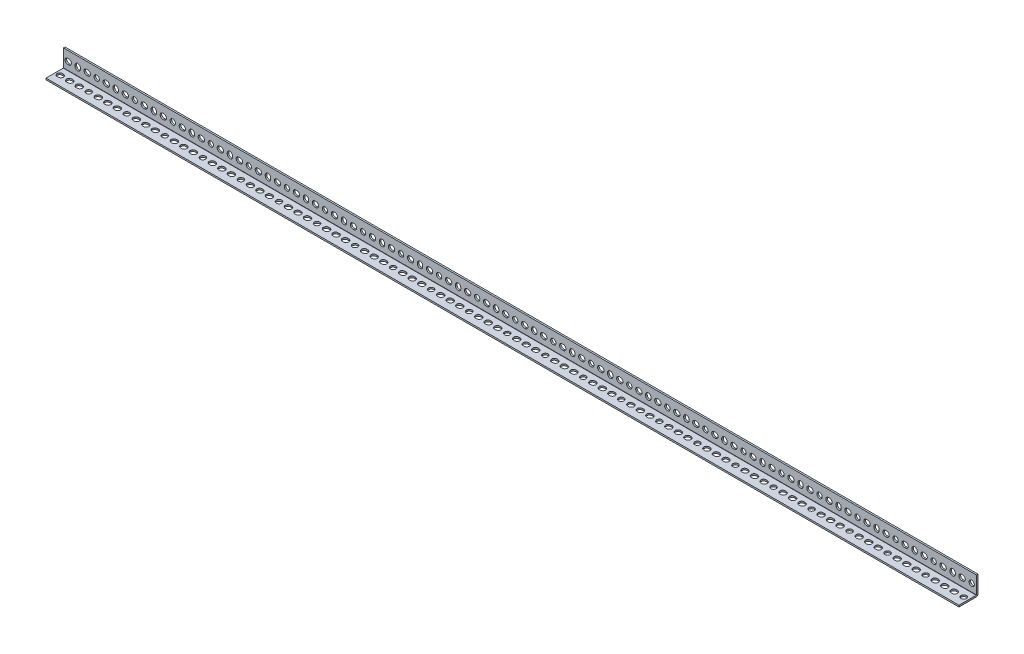
SolidWorks part; units mm, degrees
ref_plane "Front Plane" through (0, 0, 0) normal (0, 0, 1) x (1, 0, 0)
ref_plane "Top Plane" through (0, 0, 0) normal (0, 1, 0) x (1, 0, 0)
ref_plane "Right Plane" through (0, 0, 0) normal (1, 0, 0) x (0, 0, -1)
sketch "Sketch1" plane through (0, 0, 0) normal (1, 0, 0) x (0, 0, -1)
  line L0 (-19.05, -15.875) -> (15.875, -15.875) construction
  line L1 (15.875, -15.875) -> (15.875, 19.05) construction
  line L2 (15.875, 19.05) -> (19.05, 19.05) construction
  line L3 (19.05, 19.05) -> (19.05, -19.05) construction
  line L4 (19.05, -19.05) -> (-19.05, -19.05) construction
  line L5 (-19.05, -19.05) -> (-19.05, -15.875) construction
  line L6 (0, -19.05) -> (0, 19.05) construction
  line L7 (19.05, 0) -> (-19.05, 0) construction
  arc A0 (15.494, -15.875) -> (15.875, -15.494) centre (15.494, -15.494) ccw construction
  dimension "D1" = 0.381
  dimension "Thickness | T" = 3.175
  dimension "Width (B)" = 38.1
  dimension "Width (A)" = 38.1
sketch "Sketch2" plane through (0, 0, 0) normal (0, 0, 1) x (1, 0, 0)
  line L0 (-914.4, 0) -> (914.4, 0) construction
  line L1 (-914.4, 19.05) -> (914.4, 19.05) construction
  line L2 (-914.4, 19.05) -> (-914.4, -19.05) construction
  line L3 (-914.4, -19.05) -> (914.4, -19.05) construction
  line L4 (914.4, 19.05) -> (914.4, -19.05) construction
  line L5 (0, 19.05) -> (0, -19.05) construction
  line L6 (886.841, 0) -> (884.809, 0) construction
  line L7 (-914.4, -15.875) -> (914.4, -15.875) construction
  line L8 (886.841, -5.334) -> (884.809, -5.334) construction
  line L9 (886.841, 5.334) -> (884.809, 5.334) construction
  line L10 (866.775, -1.016) -> (866.775, 1.016) construction
  line L11 (861.441, -1.016) -> (861.441, 1.016) construction
  line L12 (872.109, -1.016) -> (872.109, 1.016) construction
  line L14 (848.741, 0) -> (846.709, 0) construction
  line L15 (848.741, -5.334) -> (846.709, -5.334) construction
  line L16 (848.741, 5.334) -> (846.709, 5.334) construction
  circle A0 centre (904.875, 0) radius 5.334 construction
  arc A2 (886.841, -5.334) -> (886.841, 5.334) centre (886.841, 0) ccw construction
  arc A3 (884.809, 5.334) -> (884.809, -5.334) centre (884.809, 0) ccw construction
  arc A4 (861.441, -1.016) -> (872.109, -1.016) centre (866.775, -1.016) ccw construction
  arc A5 (872.109, 1.016) -> (861.441, 1.016) centre (866.775, 1.016) ccw construction
  arc A6 (848.741, -5.334) -> (848.741, 5.334) centre (848.741, 0) ccw construction
  arc A7 (846.709, 5.334) -> (846.709, -5.334) centre (846.709, 0) ccw construction
  point P15 (819.15, 0)
  point P16 (-819.15, 0)
  point P17 (885.825, 0)
  point P24 (910.209, 0)
  point P26 (866.775, 0)
  point P37 (847.725, 0)
  dimension "Mounting Hole Diameter" = 10.668
  dimension "Length | L" = 1828.8
  dimension "D1" = 9.525
  dimension "D2" = 85.725
  dimension "D3" = 12.7
  dimension "D4" = 19.05
  dimension "Mounting Hole Center to Center" = 19.05
  dimension "D5" = 19.05
  dimension "D7" = 19.05
sketch "Sketch3" plane through (0, 0, 0) normal (0, 1, 0) x (1, 0, 0)
  line L0 (886.841, 0) -> (884.809, 0) construction
  line L1 (-914.4, 19.05) -> (914.4, 19.05) construction
  line L2 (-914.4, 19.05) -> (-914.4, -19.05) construction
  line L3 (-914.4, -19.05) -> (914.4, -19.05) construction
  line L4 (914.4, 19.05) -> (914.4, -19.05) construction
  line L5 (-914.4, 15.875) -> (914.4, 15.875) construction
  line L6 (886.841, -5.334) -> (884.809, -5.334) construction
  line L7 (865.759, 0) -> (867.791, 0) construction
  line L8 (886.841, 5.334) -> (884.809, 5.334) construction
  line L12 (846.709, 0) -> (848.741, 0) construction
  line L13 (846.709, 5.334) -> (848.741, 5.334) construction
  line L14 (846.709, -5.334) -> (848.741, -5.334) construction
  line L16 (886.841, 5.334) -> (904.875, 5.334) construction
  line L17 (865.759, 5.334) -> (867.791, 5.334) construction
  line L18 (865.759, -5.334) -> (867.791, -5.334) construction
  circle A0 centre (904.875, 0) radius 5.334 construction
  arc A2 (886.841, -5.334) -> (886.841, 5.334) centre (886.841, 0) ccw construction
  arc A3 (884.809, 5.334) -> (884.809, -5.334) centre (884.809, 0) ccw construction
  arc A6 (846.709, 5.334) -> (846.709, -5.334) centre (846.709, 0) ccw construction
  arc A7 (848.741, -5.334) -> (848.741, 5.334) centre (848.741, 0) ccw construction
  arc A10 (865.759, 5.334) -> (865.759, -5.334) centre (865.759, 0) ccw construction
  arc A11 (867.791, -5.334) -> (867.791, 5.334) centre (867.791, 0) ccw construction
  point P9 (885.825, 0)
  point P21 (910.209, 0)
  point P28 (866.775, 0)
  point P42 (847.725, 0)
  dimension "D1" = 19.05
sketch "Sketch4" plane through (0, 0, 0) normal (1, 0, 0) x (0, 0, -1)
  line L0 (-19.05, -15.875) -> (15.494, -15.875)
  line L1 (15.875, -15.494) -> (15.875, 19.05)
  line L2 (15.875, 19.05) -> (19.05, 19.05)
  line L3 (19.05, 19.05) -> (19.05, -15.494)
  line L4 (15.494, -19.05) -> (-19.05, -19.05)
  line L5 (-19.05, -19.05) -> (-19.05, -15.875)
  arc A0 (15.494, -15.875) -> (15.875, -15.494) centre (15.494, -15.494) ccw
  arc A1 (19.05, -15.494) -> (15.494, -19.05) centre (15.494, -15.494) cw
extrude "Boss-Extrude1" add sketch "Sketch4" along normal up to vertex (914.4 mm away) and the other way up to vertex (914.4 mm away) up to point (914.4, 0, 0) other way up to point (-914.4, 0, 0)
sketch "Sketch5" plane through (0, 0, 0) normal (0, 0, 1) x (1, 0, 0)
  line L0 (884.809, 0) -> (886.841, 0) construction
  line L1 (884.809, 5.334) -> (886.841, 5.334)
  line L2 (884.809, -5.334) -> (886.841, -5.334)
  line L3 (866.775, 1.016) -> (866.775, -1.016) construction
  line L4 (872.109, 1.016) -> (872.109, -1.016)
  line L5 (861.441, 1.016) -> (861.441, -1.016)
  line L6 (846.709, 0) -> (848.741, 0) construction
  line L7 (846.709, 5.334) -> (848.741, 5.334)
  line L8 (846.709, -5.334) -> (848.741, -5.334)
  circle A0 centre (904.875, 0) radius 5.334
  arc A1 (884.809, 5.334) -> (884.809, -5.334) centre (884.809, 0) ccw
  arc A2 (886.841, -5.334) -> (886.841, 5.334) centre (886.841, 0) ccw
  arc A3 (872.109, 1.016) -> (861.441, 1.016) centre (866.775, 1.016) ccw
  arc A4 (861.441, -1.016) -> (872.109, -1.016) centre (866.775, -1.016) ccw
  arc A5 (846.709, 5.334) -> (846.709, -5.334) centre (846.709, 0) ccw
  arc A6 (848.741, -5.334) -> (848.741, 5.334) centre (848.741, 0) ccw
  point P5 (885.825, 0)
  point P13 (866.775, 0)
  point P28 (847.725, 0)
extrude "Cut-Extrude1" cut sketch "Sketch5" against normal through all
pattern_linear "LPattern1" count 25 spacing 76.2 along (-1, 0, 0) of "Cut-Extrude1"
sketch "Sketch6" plane through (0, 0, 0) normal (0, 1, 0) x (1, 0, 0)
  line L0 (884.809, 0) -> (886.841, 0) construction
  line L1 (884.809, 5.334) -> (886.841, 5.334)
  line L2 (884.809, -5.334) -> (886.841, -5.334)
  line L3 (865.759, 0) -> (867.791, 0) construction
  line L6 (846.709, 0) -> (848.741, 0) construction
  line L7 (846.709, 5.334) -> (848.741, 5.334)
  line L8 (846.709, -5.334) -> (848.741, -5.334)
  line L11 (865.759, 5.334) -> (867.791, 5.334)
  line L12 (865.759, -5.334) -> (867.791, -5.334)
  circle A0 centre (904.875, 0) radius 5.334
  arc A1 (884.809, 5.334) -> (884.809, -5.334) centre (884.809, 0) ccw
  arc A2 (886.841, -5.334) -> (886.841, 5.334) centre (886.841, 0) ccw
  arc A5 (846.709, 5.334) -> (846.709, -5.334) centre (846.709, 0) ccw
  arc A6 (848.741, -5.334) -> (848.741, 5.334) centre (848.741, 0) ccw
  arc A9 (865.759, 5.334) -> (865.759, -5.334) centre (865.759, 0) ccw
  arc A10 (867.791, -5.334) -> (867.791, 5.334) centre (867.791, 0) ccw
  point P8 (885.825, 0)
  point P15 (866.775, 0)
  point P22 (847.725, 0)
extrude "Cut-Extrude2" cut sketch "Sketch6" against normal through all
pattern_linear "LPattern2" count 25 spacing 76.2 along (-1, 0, 0) of "Cut-Extrude2"
equation "\"D1@Sketch2\"= ( \"Length | L@Sketch2\" - \"Mounting Hole Center to Center@Sketch2\" * \"Num Holes\" ) / 2"
equation "\"Num Holes\"= int ( \"Length | L@Sketch2\" / \"Mounting Hole Center to Center@Sketch2\" ) - 1"
equation "\"D2@Sketch2\"=\"Mounting Hole Center to Center@Sketch2\"*4.5"
equation "\"D3@LPattern1\"=\"Mounting Hole Center to Center@Sketch2\"*4"
equation "\"D4@Sketch2\"=\"Mounting Hole Center to Center@Sketch2\""
equation "\"D3@LPattern2\"=\"Mounting Hole Center to Center@Sketch2\"*4"
equation "\"D7@Sketch2\"=\"Mounting Hole Center to Center@Sketch2\""
